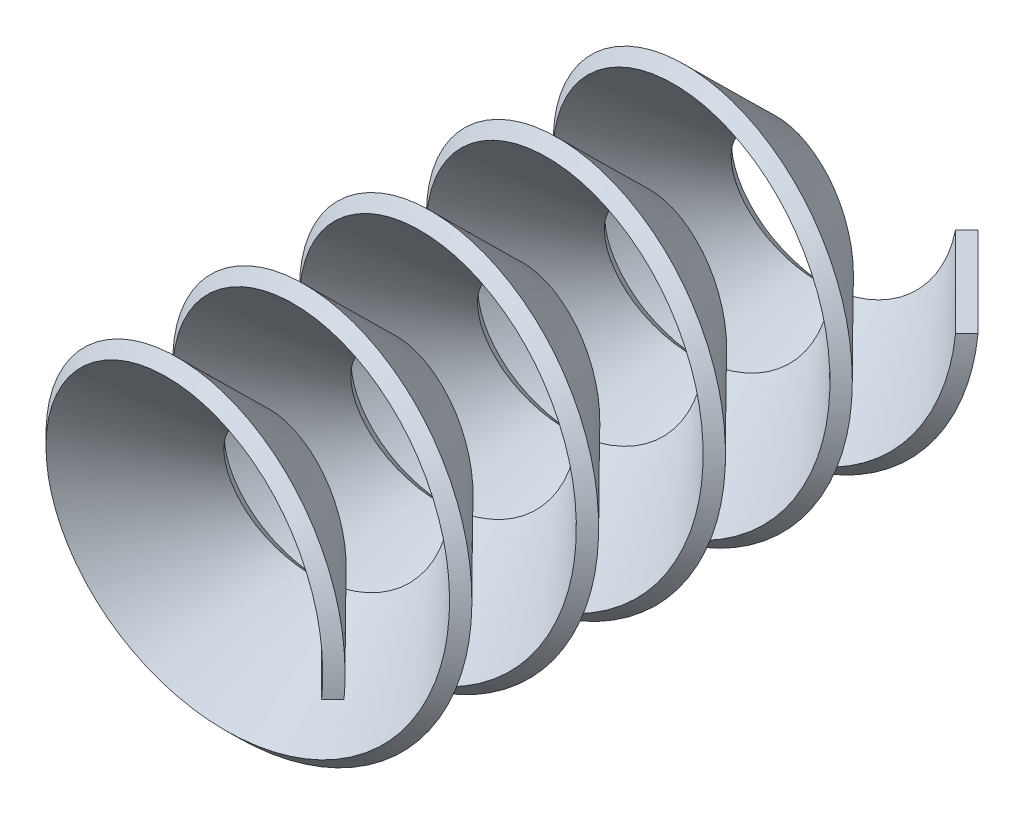
SolidWorks part; units mm, degrees
ref_plane "Vorne" through (0, 0, 0) normal (0, 0, 1) x (1, 0, 0)
ref_plane "Oben" through (0, 0, 0) normal (0, 1, 0) x (1, 0, 0)
ref_plane "Rechts" through (0, 0, 0) normal (1, 0, 0) x (0, 0, -1)
other "Massenmittelpunkt"
sketch "Skizze1" plane through (0, 0, 0) normal (0, 0, 1) x (1, 0, 0)
  circle A0 centre (0, 0) radius 2.5
  dimension "D1" = 5
curve "Spirale/Helix1" pitch 4 height 20 turns 5
sketch "Skizze2" plane through (0, 0, 0) normal (0, 1, 0) x (1, 0, 0)
  line L0 (2.5, -20) -> (5.3284, -22.8284)
  line L1 (2.5, -20) -> (2.5, -21.7221) construction
  line L2 (2.5, -20) -> (2.8536, -19.6464)
  line L3 (2.8536, -19.6464) -> (5.682, -22.4749)
  line L4 (5.682, -22.4749) -> (5.3284, -22.8284)
  spline S0 degree 3 poles (2.5, 0) (2.5, -0.0828) (2.3698, -0.2502) (1.8138, -0.4999) (0.9816, -0.75) (0, -1) (-0.9816, -1.25) (-1.8138, -1.5) (-2.3698, -1.75) (-2.5651, -2) (-2.3698, -2.25) (-1.8138, -2.5) (-0.9816, -2.75) (0, -3) (0.9816, -3.25) (1.8138, -3.5) (2.3698, -3.75) (2.5651, -4) (2.3698, -4.25) (1.8138, -4.5) (0.9816, -4.75) (0, -5) (-0.9816, -5.25) (-1.8138, -5.5) (-2.3698, -5.75) (-2.5651, -6) (-2.3698, -6.25) (-1.8138, -6.5) (-0.9816, -6.75) (0, -7) (0.9816, -7.25) (1.8138, -7.5) (2.3698, -7.75) (2.5651, -8) (2.3698, -8.25) (1.8138, -8.5) (0.9816, -8.75) (0, -9) (-0.9816, -9.25) (-1.8138, -9.5) (-2.3698, -9.75) (-2.5651, -10) (-2.3698, -10.25) (-1.8138, -10.5) (-0.9816, -10.75) (0, -11) (0.9816, -11.25) (1.8138, -11.5) (2.3698, -11.75) (2.5651, -12) (2.3698, -12.25) (1.8138, -12.5) (0.9816, -12.75) (0, -13) (-0.9816, -13.25) (-1.8138, -13.5) (-2.3698, -13.75) (-2.5651, -14) (-2.3698, -14.25) (-1.8138, -14.5) (-0.9816, -14.75) (0, -15) (0.9816, -15.25) (1.8138, -15.5) (2.3698, -15.75) (2.5651, -16) (2.3698, -16.25) (1.8138, -16.5) (0.9816, -16.75) (0, -17) (-0.9816, -17.25) (-1.8138, -17.5) (-2.3698, -17.75) (-2.5651, -18) (-2.3698, -18.25) (-1.8138, -18.5) (-0.9816, -18.75) (0, -19) (0.9816, -19.25) (1.8138, -19.5001) (2.3698, -19.7498) (2.5, -19.9172) (2.5, -20) knots 0 0 0 0 0.0125 0.025 0.0375 0.05 0.0625 0.075 0.0875 0.1 0.1125 0.125 0.1375 0.15 0.1625 0.175 0.1875 0.2 0.2125 0.225 0.2375 0.25 0.2625 0.275 0.2875 0.3 0.3125 0.325 0.3375 0.35 0.3625 0.375 0.3875 0.4 0.4125 0.425 0.4375 0.45 0.4625 0.475 0.4875 0.5 0.5125 0.525 0.5375 0.55 0.5625 0.575 0.5875 0.6 0.6125 0.625 0.6375 0.65 0.6625 0.675 0.6875 0.7 0.7125 0.725 0.7375 0.75 0.7625 0.775 0.7875 0.8 0.8125 0.825 0.8375 0.85 0.8625 0.875 0.8875 0.9 0.9125 0.925 0.9375 0.95 0.9625 0.975 0.9875 1 1 1 1 construction
  dimension "D1" = 45
  dimension "D2" = 4
  dimension "D3" = 0.5
sweep "Austragung1" add profiles "Skizze2" path "Spirale/Helix1"
